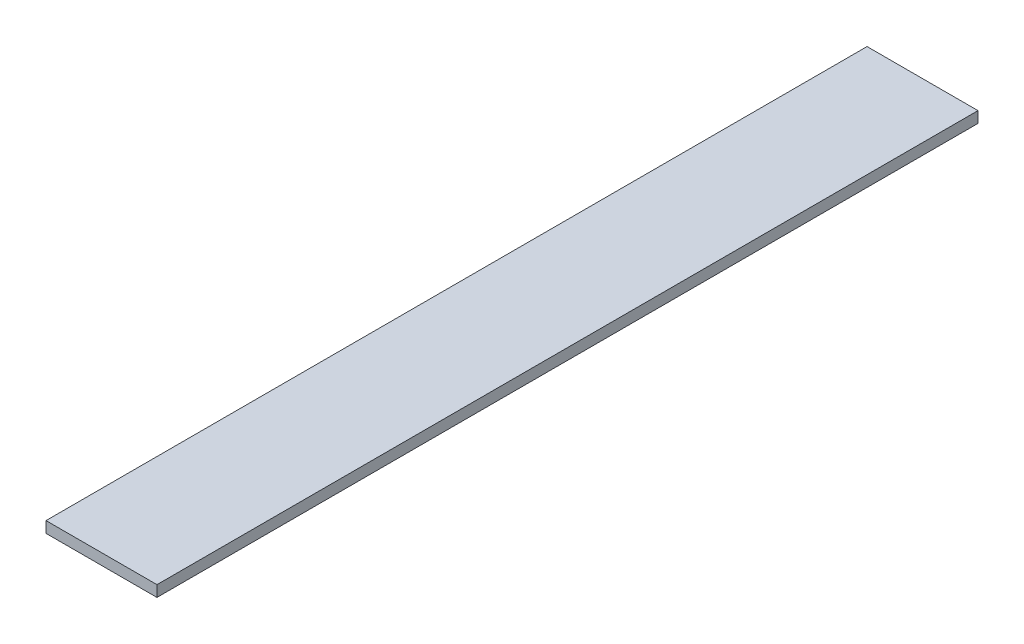
SolidWorks part; units mm, degrees
ref_plane "Front Plane" through (0, 0, 0) normal (0, 0, 1) x (1, 0, 0)
ref_plane "Top Plane" through (0, 0, 0) normal (0, 1, 0) x (1, 0, 0)
ref_plane "Right Plane" through (0, 0, 0) normal (1, 0, 0) x (0, 0, -1)
sketch "Sketch1" plane through (0, 0, 0) normal (0, 1, 0) x (1, 0, 0)
  line L0 (0, 0) -> (-50, 0)
  line L1 (-50, 0) -> (-50, 370)
  line L2 (-50, 370) -> (0, 370)
  line L3 (0, 370) -> (0, 0)
  dimension "D1" = 370
  dimension "D2" = 50
extrude "Boss-Extrude1" add sketch "Sketch1" along normal blind 5
